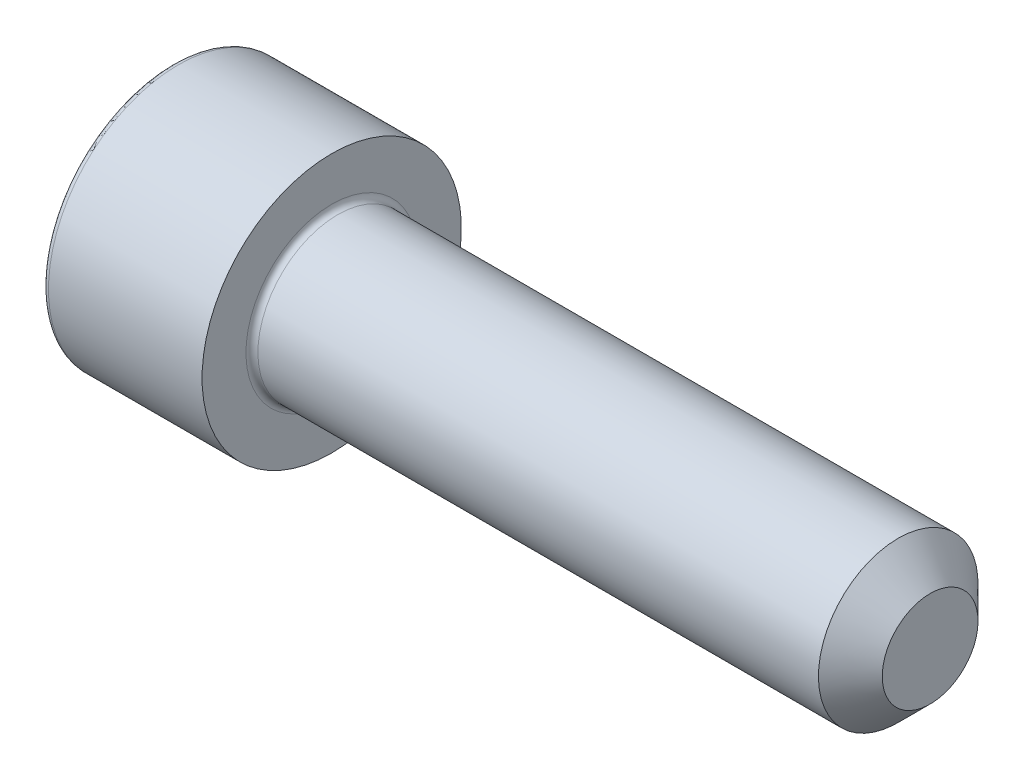
SolidWorks part; units mm, degrees
ref_plane "Спереди" through (0, 0, 0) normal (0, 0, 1) x (1, 0, 0)
ref_plane "Сверху" through (0, 0, 0) normal (0, 1, 0) x (1, 0, 0)
ref_plane "Справа" through (0, 0, 0) normal (1, 0, 0) x (0, 0, -1)
sketch "Эскиз1" plane through (0, 0, 0) normal (0, 0, 1) x (1, 0, 0)
  line L0 (0, 0) -> (0, 6.5)
  line L1 (0, 6.5) -> (8, 6.5)
  line L2 (8, 6.5) -> (8, 4)
  line L3 (8, 4) -> (38, 4)
  line L4 (38, 4) -> (38, 0)
  line L5 (38, 0) -> (0, 0) construction
  line L6 (0, 0) -> (38, 0)
  dimension "D1" = 13
  dimension "D2" = 8
  dimension "D3" = 8
  dimension "D4" = 30
revolve "Повернуть1" add sketch "Эскиз1" angle 360 about L5
cosmetic thread "Условное изображение резьбы1" parameters "D2"=6.619
sketch "Эскиз2" plane through (0, 0, 0) normal (-1, 0, 0) x (0, 0, 1)
  line L1 (-1.7321, 3) -> (-3.4641, 0)
  line L2 (-3.4641, 0) -> (-1.7321, -3)
  line L3 (-1.7321, -3) -> (1.7321, -3)
  line L4 (1.7321, -3) -> (3.4641, 0)
  line L5 (3.4641, 0) -> (1.7321, 3)
  line L6 (1.7321, 3) -> (-1.7321, 3)
  circle A0 centre (0, 0) radius 3 construction
  dimension "D1" = 6
extrude "Вырез-Вытянуть1" cut sketch "Эскиз2" against normal blind 2.5
fillet "Скругление1" radius 0.3 2 edges at (0, 6.5, 0) (8, 4, 0)
chamfer "Фаска1" distance 1.6 angle 45 1 edges at (38, 4, 0)
